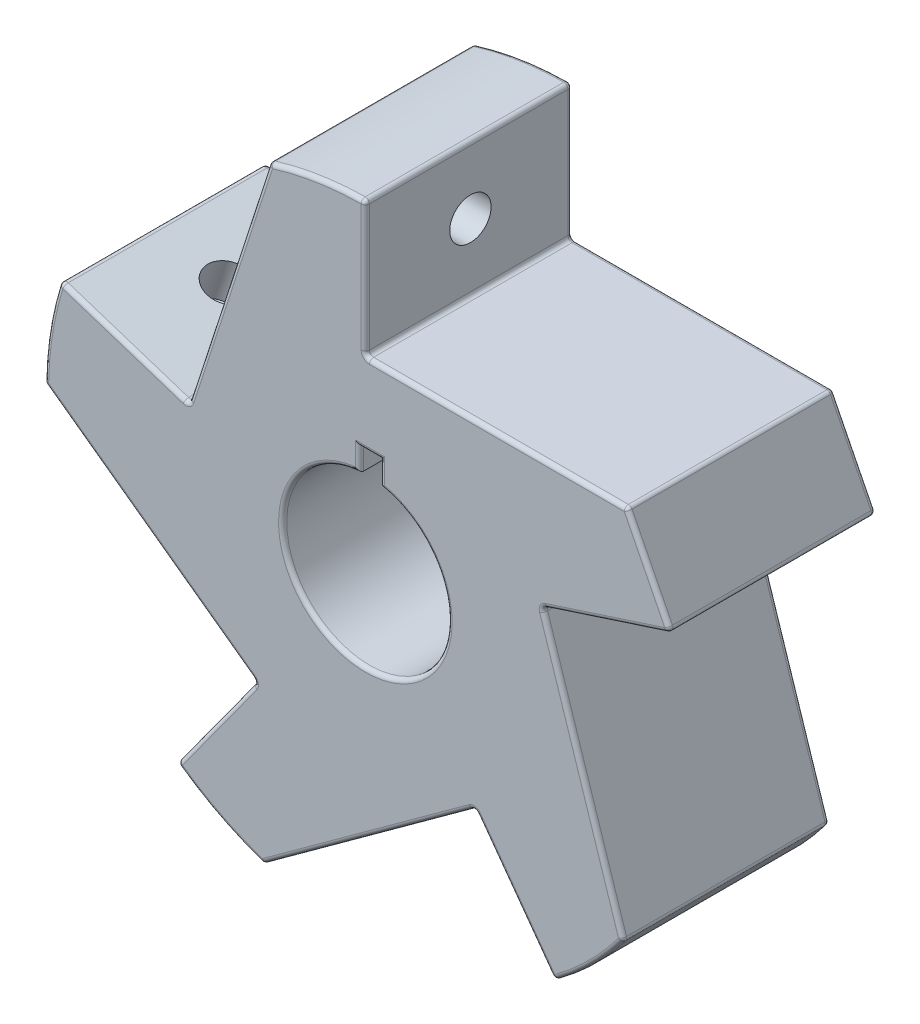
SolidWorks part; units mm, degrees
ref_plane "Front Plane" through (0, 0, 0) normal (0, 0, 1) x (1, 0, 0)
ref_plane "Top Plane" through (0, 0, 0) normal (0, 1, 0) x (1, 0, 0)
ref_plane "Right Plane" through (0, 0, 0) normal (1, 0, 0) x (0, 0, -1)
sketch "Sketch1" plane through (0, 0, 0) normal (0, 0, 1) x (1, 0, 0)
  line L0 (0, 45) -> (63.2456, 45)
  line L1 (0, 45) -> (0, 77.6209)
  line L2 (0, 0) -> (0, 45) construction
  line L3 (0, 0) -> (73.8218, 23.9862) construction
  line L4 (63.2456, 45) -> (73.8218, 23.9862)
  line L5 (42.7975, 13.9058) -> (73.8218, 23.9862)
  line L6 (0, 0) -> (-95.2176, 30.9381) construction
  line L7 (26.4503, -36.4058) -> (45.6244, -62.7966)
  line L8 (-26.4503, -36.4058) -> (-45.6244, -62.7966)
  line L9 (-42.7975, 13.9058) -> (-73.8218, 23.9862)
  line L10 (42.7975, 13.9058) -> (62.3415, -46.2443)
  line L11 (26.4503, -36.4058) -> (-24.7164, -73.5806)
  line L12 (-26.4503, -36.4058) -> (-77.6171, 0.769)
  line L13 (-42.7975, 13.9058) -> (-23.2536, 74.0559)
  circle A0 centre (0, 0) radius 45
  circle A1 centre (0, 0) radius 77.6209
  circle A2 centre (0, 0) radius 20
  point P19 (0, 0)
  point P27 (0, 0)
  dimension "D1" = 72
  dimension "D2" = 72
  dimension "D3" = 5
  dimension "D4" = 5
extrude "Boss-Extrude2" add sketch "Sketch1" along normal blind 50 contours L1 A1 L13 A0 | L9 A1 L12 A0 | A0 L5 L4 L0 | L8 A1 L11 A0 | L7 A1 L10 A0 | A0 A2
sketch "Sketch2" plane through (0, 0, 0) normal (0, 0, 1) x (1, 0, 0)
  line L5 (-1.408, 25.4744) -> (3.592, 25.4744)
  line L6 (-1.408, 25.4744) -> (-1.408, 14.4744)
  line L7 (-1.408, 14.4744) -> (3.592, 14.4744)
  line L8 (3.592, 25.4744) -> (3.592, 14.4744)
  dimension "D1" = 5
  dimension "D2" = 11
extrude "Cut-Extrude3" cut sketch "Sketch2" along normal blind 60
fillet "Fillet1" radius 1 50 edges at (36.0374, -49.6012, 0) (26.4503, -36.4058, 25) (0.867, -54.9932, 0) (58.3097, 18.946, 0) (-11.7626, 76.7244, 0) (-58.3097, 18.946, 0) (-73.8218, 23.9862, 25) (-76.6041, 12.5222, 0) (-23.2536, 74.0559, 25) (-42.7975, 13.9058, 25) (-33.0256, 43.9808, 0) (-36.0374, -49.6012, 0) (-77.6171, 0.769, 25) (-26.4503, -36.4058, 25) (-52.0337, -17.8184, 0) (-45.6244, -62.7966, 25) (-24.7164, -73.5806, 25) (-35.5813, -68.9853, 0) (45.6244, -62.7966, 25) (54.6137, -55.1575, 0) (3.592, 22.5746, 50) (1.092, 25.4744, 50) (-1.408, 22.7124, 50) (-1.1006, -19.9697, 50) (58.3097, 18.946, 50) (54.6137, -55.1575, 50) (36.0374, -49.6012, 50) (0.867, -54.9932, 50) (-35.5813, -68.9853, 50) (-36.0374, -49.6012, 50) (-52.0337, -17.8184, 50) (-76.6041, 12.5222, 50) (-58.3097, 18.946, 50) (-33.0256, 43.9808, 50) (-11.7626, 76.7244, 50) (62.3415, -46.2443, 25) (52.5695, -16.1693, 50) (42.7975, 13.9058, 25) (52.5695, -16.1693, 0) (73.8218, 23.9862, 25) (68.5337, 34.4931, 50) (68.5337, 34.4931, 0) (63.2456, 45, 25) (31.6228, 45, 50) (31.6228, 45, 0) (0, 45, 25) (0, 61.3104, 50) (0, 77.6209, 25) (0, 61.3104, 0) (-1.1006, -19.9697, 0)
sketch "Sketch3" plane through (0, 0, 0) normal (1, 0, 0) x (0, 0, -1)
  line L0 (-50, 61.3072) -> (0.8274, 61.3072) construction
  line L1 (-50, 46) -> (-50, 76.6143) construction
  line L2 (-25, 77.6143) -> (-25, 44.4496) construction
  line L3 (-1, 77.6143) -> (-49, 77.6143) construction
  line L4 (-1, 44.4496) -> (-49, 44.4496) construction
  circle A0 centre (-24.5863, 61.3072) radius 5.0036
extrude "Cut-Extrude4" cut sketch "Sketch3" against normal blind 10
sketch "Sketch4" plane through (0, 0, 0) normal (0.309, -0.9511, 0) x (0.9511, 0.309, 0)
  line L0 (76.4559, 25) -> (44.5743, 25) construction
  line L1 (76.4559, 1) -> (76.4559, 49) construction
  line L2 (44.5743, 1) -> (44.5743, 49) construction
  line L3 (44.5743, 25) -> (60.5151, 25) construction
  line L4 (60.5151, 25) -> (60.5151, 50.5365) construction
  circle A0 centre (60.5151, 25) radius 5
extrude "Cut-Extrude5" cut sketch "Sketch4" against normal blind 10
sketch "Sketch5" plane through (0, 0, 0) normal (-0.809, -0.5878, 0) x (0, 0, 1)
  line L0 (25, -76.6143) -> (25, -44.5743) construction
  line L1 (1, -76.6143) -> (49, -76.6143) construction
  line L2 (1, -44.5743) -> (49, -44.5743) construction
  line L3 (25, -44.5743) -> (25, -60.5943) construction
  line L4 (25, -60.5943) -> (50.609, -60.5943) construction
  circle A0 centre (25, -60.5943) radius 5
extrude "Cut-Extrude6" cut sketch "Sketch5" against normal blind 10
sketch "Sketch6" plane through (0, 0, 0) normal (-0.809, 0.5878, 0) x (0, 0, 1)
  line L0 (25, -45) -> (25, -77.6143) construction
  line L1 (1, -45) -> (49, -45) construction
  line L2 (1, -77.6143) -> (49, -77.6143) construction
  line L3 (25, -77.6143) -> (25, -61.3072) construction
  line L4 (25, -61.3072) -> (52.8179, -61.3072) construction
  circle A0 centre (25, -61.3072) radius 5
extrude "Cut-Extrude7" cut sketch "Sketch6" against normal blind 10
sketch "Sketch7" plane through (0, 0, 0) normal (0.309, 0.9511, 0) x (0.9511, -0.309, 0)
  line L0 (-76.6143, -25) -> (-46, -25) construction
  line L1 (-76.6143, -1) -> (-76.6143, -49) construction
  line L2 (-46, -49) -> (-46, -1) construction
  line L3 (-61.3072, -25) -> (-61.3072, 0.7285) construction
  circle A0 centre (-61.3072, -25) radius 5
extrude "Cut-Extrude8" cut sketch "Sketch7" against normal blind 10
